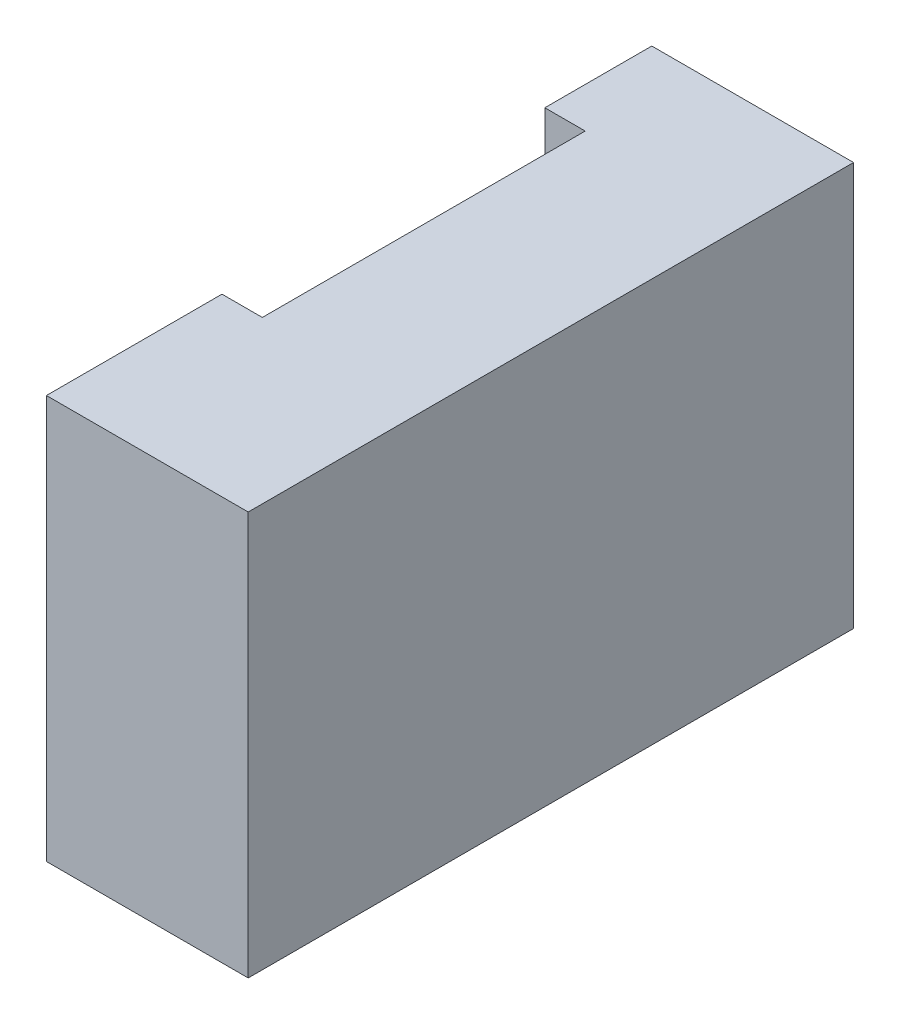
SolidWorks part; units mm, degrees
ref_plane "Front Plane" through (0, 0, 0) normal (0, 0, 1) x (1, 0, 0)
ref_plane "Top Plane" through (0, 0, 0) normal (0, 1, 0) x (1, 0, 0)
ref_plane "Right Plane" through (0, 0, 0) normal (1, 0, 0) x (0, 0, -1)
sketch "Sketch1" plane through (0, 0, 0) normal (0, 0, 1) x (1, 0, 0)
  line L1 (-2.5, -5) -> (2.5, -5)
  line L2 (-2.5, -5) -> (-2.5, 5)
  line L3 (-2.5, 5) -> (2.5, 5)
  line L4 (2.5, -5) -> (2.5, 5)
  line L5 (-2.5, -5) -> (2.5, 5) construction
  line L6 (-2.5, 5) -> (2.5, -5) construction
  point P0 (0, 0)
  dimension "D1" = 5
  dimension "D2" = 10
extrude "Boss-Extrude1" add sketch "Sketch1" along normal mid plane 15
sketch "Sketch4" plane through (0, 5, 0) normal (0, 1, 0) x (1, 0, 0)
  line L0 (-2.5, -7.5) -> (-2.5, 7.5) construction
  line L1 (-2.5, 4.85) -> (-1.5, 4.85)
  line L2 (-2.5, 4.85) -> (-2.5, -3.15)
  line L3 (-2.5, -3.15) -> (-1.5, -3.15)
  line L4 (-1.5, 4.85) -> (-1.5, -3.15)
  line L5 (2.5, -7.5) -> (-2.5, -7.5) construction
  dimension "D1" = 4.35
  dimension "D2" = 8
  dimension "D3" = 1
extrude "Cut-Extrude2" cut sketch "Sketch4" against normal through all
sketch "Sketch3" plane through (2.5, 0, 0) normal (1, 0, 0) x (0, 0, -1)
  line L0 (-7.5, -5) -> (-7.5, 5) construction
  circle A0 centre (-4.5, 0) radius 1.75
  circle A1 centre (1.5, 0) radius 1.75
  dimension "D2" = 3.5
  dimension "D1" = 6
  dimension "D3" = 3
